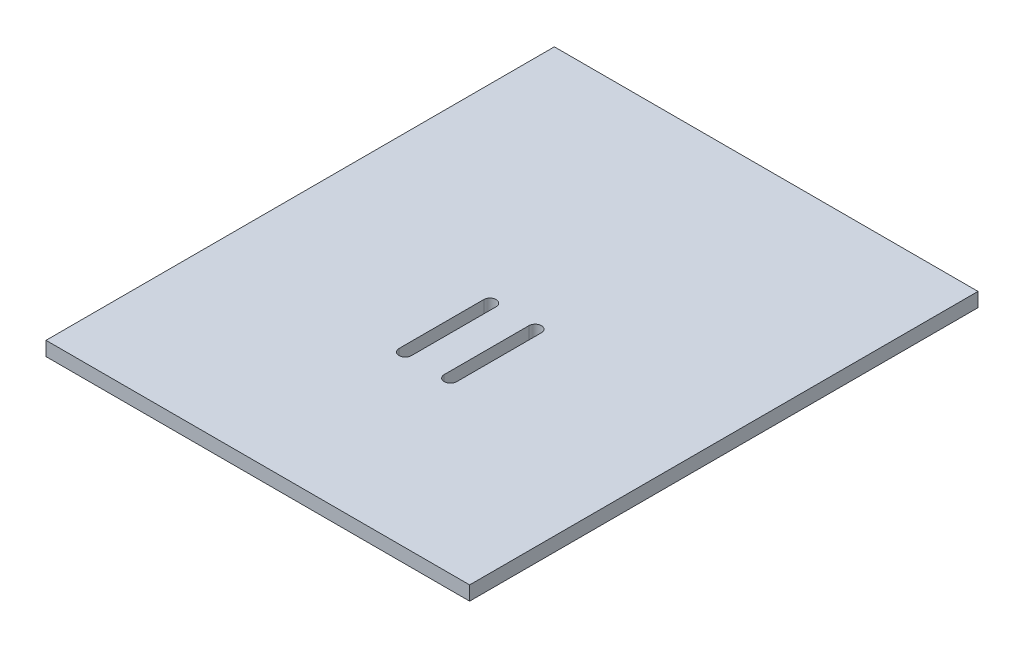
SolidWorks part; units mm, degrees
ref_plane "Front Plane" through (0, 0, 0) normal (0, 0, 1) x (1, 0, 0)
ref_plane "Top Plane" through (0, 0, 0) normal (0, 1, 0) x (1, 0, 0)
ref_plane "Right Plane" through (0, 0, 0) normal (1, 0, 0) x (0, 0, -1)
sketch "Sketch1" plane through (0, 0, 0) normal (0, 1, 0) x (1, 0, 0)
  line L1 (-95.25, 114.3) -> (95.25, 114.3)
  line L2 (-95.25, 114.3) -> (-95.25, -114.3)
  line L3 (-95.25, -114.3) -> (95.25, -114.3)
  line L4 (95.25, 114.3) -> (95.25, -114.3)
  line L5 (-95.25, 114.3) -> (95.25, -114.3) construction
  line L6 (-95.25, -114.3) -> (95.25, 114.3) construction
  point P0 (0, 0)
  dimension "D1" = 228.6
  dimension "D2" = 190.5
extrude "Boss-Extrude1" add sketch "Sketch1" along normal blind 6.35
sketch "Sketch2" plane through (0, 6.35, 0) normal (0, 1, 0) x (1, 0, 0)
  line L0 (-9.906, 0) -> (-9.906, -38.1) construction
  line L1 (-7.112, 0) -> (-7.112, -38.1)
  line L2 (-12.7, 0) -> (-12.7, -38.1)
  line L3 (10.414, 0) -> (10.414, -38.1) construction
  line L4 (13.208, 0) -> (13.208, -38.1)
  line L5 (7.62, 0) -> (7.62, -38.1)
  line L6 (-95.25, 114.3) -> (-95.25, -114.3) construction
  line L7 (-95.25, -114.3) -> (95.25, -114.3) construction
  arc A0 (-7.112, 0) -> (-12.7, 0) centre (-9.906, 0) ccw
  arc A1 (-12.7, -38.1) -> (-7.112, -38.1) centre (-9.906, -38.1) ccw
  arc A2 (13.208, 0) -> (7.62, 0) centre (10.414, 0) ccw
  arc A3 (7.62, -38.1) -> (13.208, -38.1) centre (10.414, -38.1) ccw
  point P2 (-9.906, -19.05)
  point P7 (10.414, -19.05)
  point P14 (-9.906, 2.794)
  point P15 (10.414, 2.794)
  dimension "D1" = 2.794
  dimension "D2" = 38.1
  dimension "D3" = 20.32
  dimension "D4" = 82.55
  dimension "D5" = 76.2
extrude "Cut-Extrude1" cut sketch "Sketch2" against normal up to next
